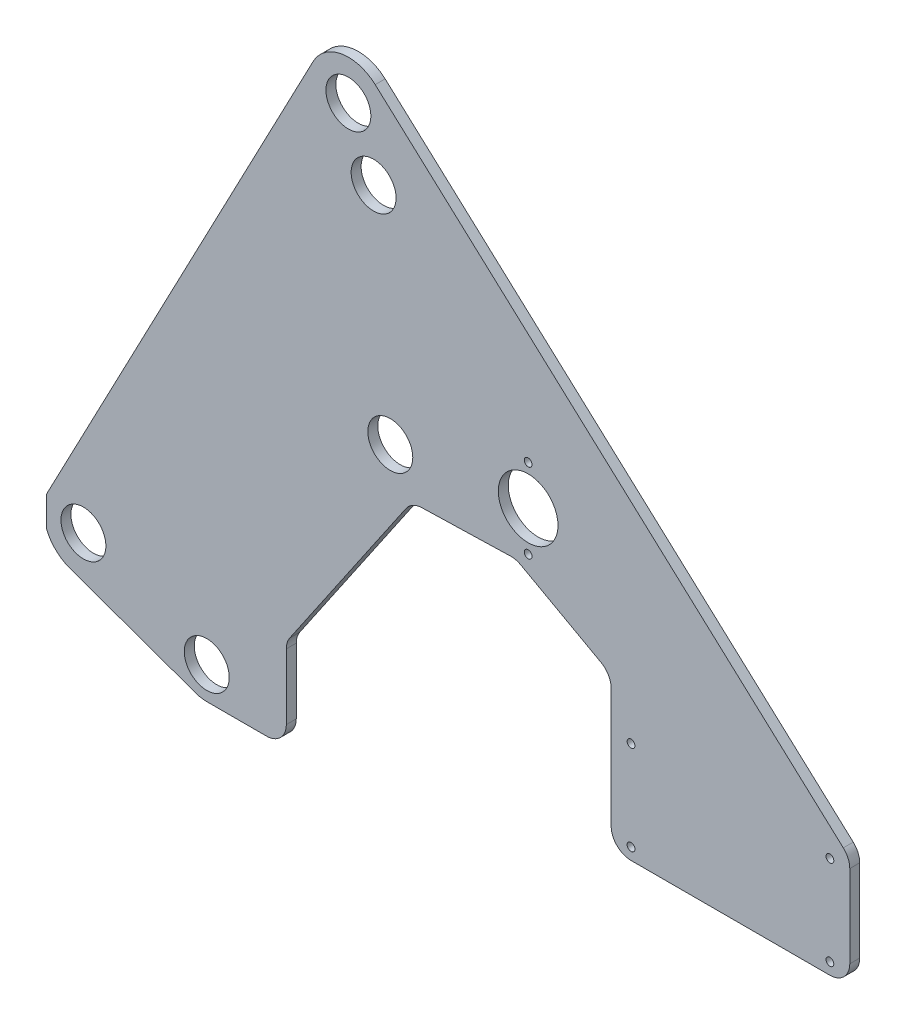
SolidWorks part; units mm, degrees
ref_plane "Front Plane" through (0, 0, 0) normal (0, 0, 1) x (1, 0, 0)
ref_plane "Top Plane" through (0, 0, 0) normal (0, 1, 0) x (1, 0, 0)
ref_plane "Right Plane" through (0, 0, 0) normal (1, 0, 0) x (0, 0, -1)
sketch "Model" plane through (0, 0, 0) normal (0, 0, 1) x (1, 0, 0)
  line L0 (71.3681, -9.525) -> (71.3681, 43.162)
  line L1 (-201.9337, 106.0953) -> (-145.2781, 107.6333)
  line L2 (-286.27, -8.1018) -> (-212.0775, 100.5612)
  line L3 (-288.4816, -57.15) -> (-288.4816, -15.2631)
  line L4 (-271.3307, 318.2291) -> (-440.5556, -4.1587)
  line L5 (-441.7893, -6.8892) -> (-441.7893, -25.0386)
  line L6 (-138.7956, 106.0563) -> (-87.5941, 77.7906)
  line L7 (-426.6215, -39.8795) -> (-346.2033, -68.6492)
  line L8 (-81.0319, 66.6723) -> (-81.0319, -9.525)
  line L9 (-339.2816, -69.85) -> (-301.1816, -69.85)
  line L10 (-68.3319, -22.225) -> (58.6681, -22.225)
  line L11 (67.226, 52.5456) -> (-231.7249, 325.1911)
  circle A0 centre (-68.3319, 42.418) radius 2.4892
  arc A1 (-440.5556, -4.1587) -> (-441.7893, -6.8892) centre (-418.0657, -15.9639) ccw
  arc A2 (-231.7249, 325.1911) -> (-271.3307, 318.2291) centre (-248.8407, 306.4239) ccw
  circle A3 centre (-134.0441, 114.3) radius 2.4892
  circle A4 centre (58.6681, -14.732) radius 2.4892
  arc A5 (71.3681, 43.162) -> (67.226, 52.5456) centre (58.6681, 43.162) ccw
  circle A6 centre (-68.3319, 42.418) radius 2.4892
  arc A7 (58.6681, -22.225) -> (71.3681, -9.525) centre (58.6681, -9.525) ccw
  arc A8 (-201.9337, 106.0953) -> (-212.0775, 100.5612) centre (-201.5891, 93.3999) ccw
  circle A9 centre (-339.2816, -49.3014) radius 14.351
  circle A10 centre (-418.0657, -15.9639) radius 14.351
  arc A11 (-138.7956, 106.0563) -> (-145.2781, 107.6333) centre (-144.9335, 94.938) ccw
  circle A12 centre (-222.0793, 130.9577) radius 14.351
  arc A13 (-286.27, -8.1018) -> (-288.4816, -15.2631) centre (-275.7816, -15.2631) ccw
  arc A14 (-81.0319, 66.6723) -> (-87.5941, 77.7906) centre (-93.7319, 66.6723) ccw
  circle A15 centre (-134.0441, 139.7) radius 19.05
  circle A16 centre (-68.3319, -14.732) radius 2.4892
  arc A17 (-346.2033, -68.6492) -> (-339.2816, -69.85) centre (-339.2816, -49.3014) ccw
  arc A18 (-81.0319, -9.525) -> (-68.3319, -22.225) centre (-68.3319, -9.525) ccw
  arc A19 (-301.1816, -69.85) -> (-288.4816, -57.15) centre (-301.1816, -57.15) ccw
  arc A20 (-441.7893, -25.0386) -> (-426.6215, -39.8795) centre (-418.0657, -15.9639) ccw
  circle A21 centre (-134.0441, 165.1) radius 2.4892
  circle A22 centre (-232.7296, 269.0861) radius 14.351
  circle A23 centre (-248.8407, 306.4239) radius 14.351
  circle A24 centre (58.6681, 42.418) radius 2.4892
extrude "Boss-Extrude1" add sketch "Model" along normal blind 6.35 contours L5 A20 L7 A17 L9 A19 L3 A13 L2 A8 L1 A11 L6 A14 L8 A18 L10 A7 L0 A5 L11 A2 L4 A1 A24 A23 A22 A21 A0 A3 A4 A9 A10 A12 A15 A16
